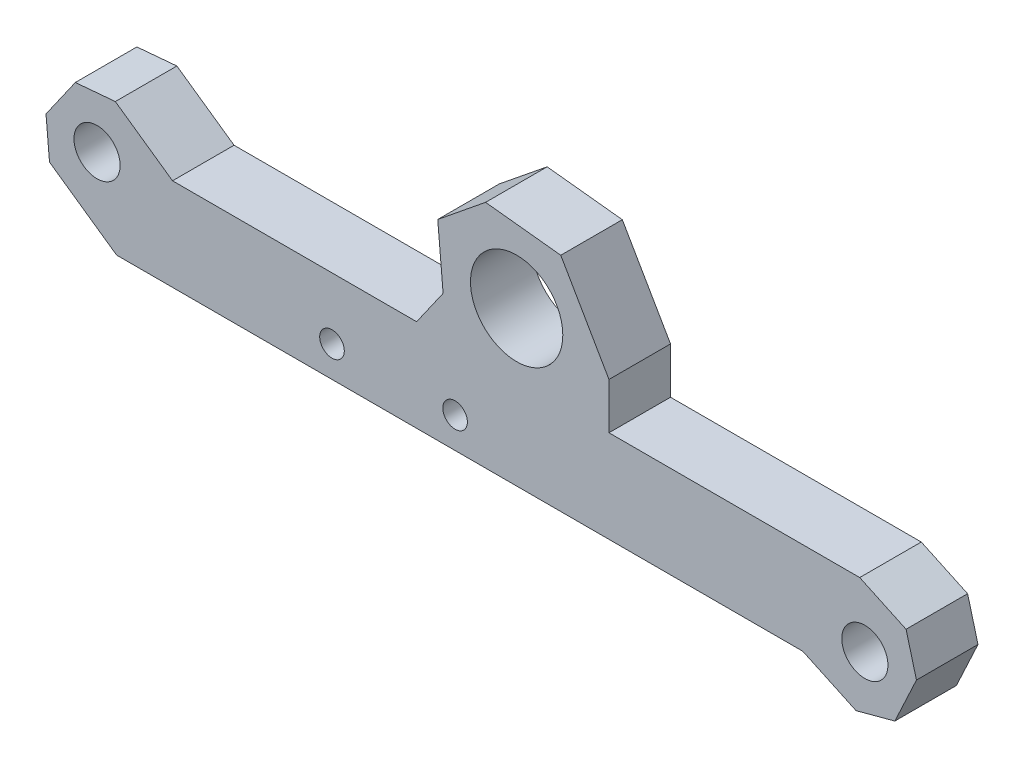
SolidWorks part; units mm, degrees
material "6061 合金"
ref_plane "前视基准面" through (0, 0, 0) normal (0, 0, 1) x (1, 0, 0)
ref_plane "上视基准面" through (0, 0, 0) normal (0, 1, 0) x (1, 0, 0)
ref_plane "右视基准面" through (0, 0, 0) normal (1, 0, 0) x (0, 0, -1)
sketch "草图1" plane through (0, 0, 0) normal (0, 0, 1) x (1, 0, 0)
  line L0 (0, 0) -> (44.5999, 0)
  line L1 (51.3487, 0.7148) -> (39.2626, 6.3507) construction
  line L2 (28.8672, 14.4261) -> (32, 9)
  line L3 (28.8672, 14.4261) -> (23.9807, 14.9595)
  line L4 (23.9807, 14.9595) -> (20.8721, 12.4422)
  line L5 (48.2963, 6) -> (32, 6)
  line L6 (3.6352, 6) -> (-1.719, 9.7491)
  line L7 (-1.719, 9.7491) -> (-5.7341, 4.015)
  line L8 (-5.7341, 4.015) -> (0, 0)
  line L9 (20.8721, 12.4422) -> (21.2207, 8.4575)
  line L10 (21.2207, 8.4575) -> (19.5, 6)
  line L11 (19.5, 6) -> (3.6352, 6)
  line L12 (26, 14) -> (26, 0) construction
  line L13 (32, 9) -> (32, 6)
  line L16 (-3.7265, 6.8821) -> (6.0461, 0.0392) construction
  line L20 (44.5999, 0) -> (49.8695, -2.4572)
  line L21 (49.8695, -2.4572) -> (52.8279, 3.8869)
  line L22 (48.2963, 6) -> (52.8279, 3.8869)
  circle A0 centre (26, 10) radius 3
  circle A2 centre (-1.2691, 5.1613) radius 1.5
  circle A3 centre (48.6298, 1.9827) radius 1.5
  dimension "D5" = 155
  dimension "D1" = 6
  dimension "D2" = 7
  dimension "D3" = 145
  dimension "D4" = 7
  dimension "D6" = 5
  dimension "D7" = 3
  dimension "D8" = 7
  dimension "D9" = 6
  dimension "D10" = 6.5
  dimension "D11" = 50
  dimension "D12" = 3
  dimension "D15" = 3
  dimension "D16" = 26
extrude "凸台-拉伸1" add sketch "草图1" along normal blind 4
hole_wizard "M2 螺纹孔1" positions "草图3" profile "草图2" tap size "M2" standard "Gb"
sketch "草图3" plane through (0, 0, 4) normal (0, 0, 1) x (1, 0, 0)
  line L0 (14, 2) -> (22, 2) construction
  line L1 (0, 0) -> (44.5999, 0) construction
  point P1 (14, 2)
  point P2 (22, 2)
  dimension "D1" = 8
  dimension "D2" = 0
  dimension "D3" = 2
  dimension "D4" = 14
sketch "草图2" plane through (14, 2, 4) normal (1, 0, 0) x (0, -1, 0)
  line L0 (0, 0) -> (0, 14.4807)
  line L1 (0, 14.4807) -> (0.8, 14)
  line L2 (0.8, 14) -> (0.8, 0)
  line L5 (0.8, 0) -> (0, 0)
  line L10 (0, 14.4807) -> (-0.8, 14) construction
  line L11 (0, -6.35) -> (0, 107.95) construction
  dimension "螺纹孔钻头直径" = 1.6
  dimension "螺纹孔钻头深度" = 14
  dimension "导头角度" = 118
cosmetic thread "孔螺蚊线1" parameters "D1"=3, "D2"=2
cosmetic thread "孔螺蚊线2" parameters "D1"=3, "D2"=2
chamfer "倒角1" distance 2 angle 40 4 edges at (49.8695, -2.4572, 2) (52.8279, 3.8869, 2) (-5.7341, 4.015, 2) (-1.719, 9.7491, 2)
